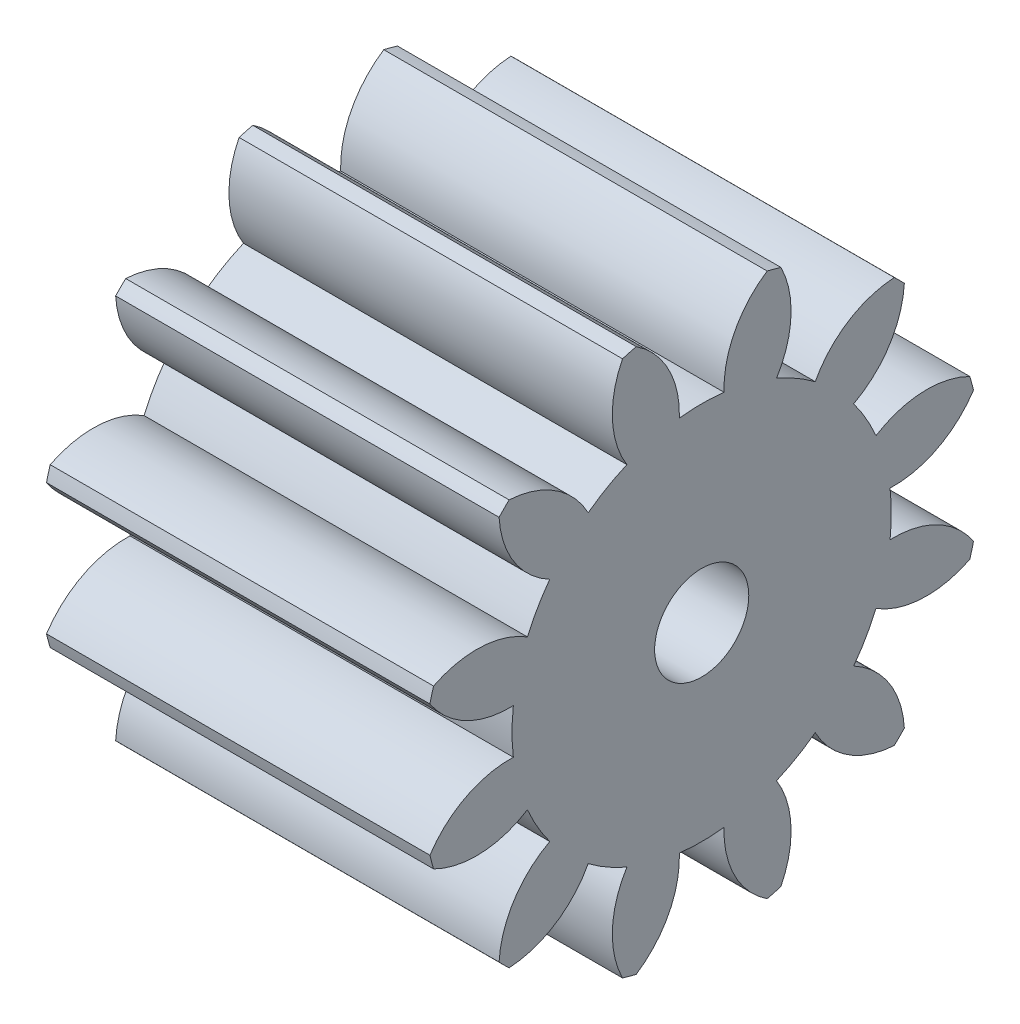
SolidWorks part; units mm, degrees
ref_plane "Plane1" through (0, 0, 0) normal (0, 0, 1) x (1, 0, 0)
ref_plane "Plane2" through (0, 0, 0) normal (0, 1, 0) x (1, 0, 0)
ref_plane "Plane3" through (0, 0, 0) normal (1, 0, 0) x (0, 0, -1)
sketch "HoldingSke" plane through (0, 0, 0) normal (0, 1, 0) x (1, 0, 0)
  line L0 (0, 0) -> (0.7825, -0.1663)
  line L1 (-15, 0) -> (100, 0) construction
  line L2 (0, 0) -> (-2.1039, 2.3779)
  line L3 (0, 0) -> (-11.863, 4.5341)
  line L4 (0, 0) -> (8.4473, 1.7955)
  line L5 (0, 0) -> (-46.8476, -17.4728)
  line L6 (0, 0) -> (-9.9476, -6.7116)
  line L7 (-2.1039, 2.3779) -> (8.6586, 51.2059)
  line L8 (-76.2, 54.61) -> (-76.1, 54.61)
  line L9 (-71.009, 38.7566) -> (-53.1078, 45.2721)
  line L10 (-76.2, 71.12) -> (104.1128, 71.12)
  line L11 (0, 0) -> (-12, 0)
  line L12 (-76.2, 101.6) -> (-76.155, 101.6)
  line L13 (24.9733, 27.94) -> (52.9518, 28.4284)
  line L14 (24.9733, 27.94) -> (24.9743, 27.94)
  line L15 (24.9733, 27.94) -> (100.4006, 29.5858)
  line L16 (-63.627, -1.25) -> (-12.827, -1.25)
  circle A0 centre (0, 0) radius 0.4
  circle A1 centre (0, 0) radius 5.9365
  circle A2 centre (0, 0) radius 37.5
  circle A3 centre (0, 0) radius 0.4
  dimension "MHD" = 11.873
  dimension "Hub_dia" = 75
  dimension "Bore" = 0.8
  dimension "MBD" = 0.8
  dimension "Num_teeth" = 12
  dimension "Pitch_radius" = 180.3128
  dimension "Pitch" = 0.8
  dimension "Width" = 12
  dimension "Overall_len" = 50
  dimension "Show_teeth" = 12
  dimension "Thickness" = 12
  dimension "OAL" = 50.0001
  dimension "T_dim" = 0.1
  dimension "Ap" = 20
  dimension "H" = 19.05
  dimension "Backlash" = 0.045
  dimension "Addendum_fac" = 1
  dimension "Dedendum_fac" = 1.25
  dimension "Clearance_fac" = 0.25
  dimension "Dedendum_add" = 0.001
  dimension "Module" = 1.25
sketch "BasProSke" plane through (0, 0, 0) normal (0, 1, 0) x (1, 0, 0)
  line L0 (-10, 0) -> (60, 0) construction
  line L1 (0, 0) -> (0, 8.75)
  line L2 (0, 0) -> (12, 0)
  line L3 (12, 0) -> (12, 8.75)
  line L4 (12, 8.75) -> (0, 8.75)
  dimension "Diameter" = 17.5
  dimension "Thickness" = 12
revolve "Base-Revolve" add sketch "BasProSke" angle 360 about L0
sketch "TooCutSke" plane through (0, 0, 0) normal (1, 0, 0) x (0, 0, -1)
  line L1 (0, 0) -> (0, 107) construction
  line L2 (0, 0) -> (-1.0576, 7.4251) construction
  line L3 (0, 0) -> (-3.8542, 14.3841) construction
  line L4 (-1.0576, 7.4251) -> (-1.9271, 7.1921) construction
  arc A0 (0.6993, 5.8952) -> (-0.6993, 5.8952) centre (0, 0) ccw
  arc A1 (2.0786, 8.5257) -> (-2.0786, 8.5257) centre (0, 0) ccw
  circle A2 centre (0, 0) radius 7.5 construction
  circle A3 centre (0, 0) radius 7.0477 construction
  arc A4 (-0.6993, 5.8952) -> (-2.0786, 8.5257) centre (-3.6975, 5.9999) ccw
  arc A5 (2.0786, 8.5257) -> (0.6993, 5.8952) centre (3.6975, 5.9999) ccw
  dimension "Root_dia" = 11.873
  dimension "Overcut_dia" = 17.5508
  dimension "Pitch_dia" = 15
  dimension "Base_dia" = 14.0954
  dimension "Flank_rad" = 3
  dimension "Half_ang" = 15
  dimension "Half_CT" = 0.9002
extrude "ToothCut" cut sketch "TooCutSke" along normal through all
fillet "Breaks" [suppressed] radius 0.025
fillet "RootFillets" [suppressed] radius 0.3135
pattern_circular "TeethCuts" count 12 every 30 about axis through (-10, 0, 0) along (1, 0, 0) of "ToothCut", "RootFillets", "Breaks"
sketch "HubNeaOneSke" plane through (0, 0, 0) normal (-1, 0, 0) x (0, 0, 1)
  circle A0 centre (0, 0) radius 5.9365
  dimension "Diameter" = 11.873
extrude "HubNearOne" [suppressed] add sketch "HubNeaOneSke" along normal blind 38.0001
sketch "HubNeaBotSke" plane through (0, 0, 0) normal (-1, 0, 0) x (0, 0, 1)
  circle A0 centre (0, 0) radius 5.9365
  dimension "Diameter" = 11.873
extrude "HubNearBoth" [suppressed] add sketch "HubNeaBotSke" along normal blind 19
ref_plane "FarPln" through (12, 0, 0) normal (1, 0, 0) x (0, 0, -1)
sketch "HubFarSke" plane through (12, 0, 0) normal (1, 0, 0) x (0, 0, -1)
  circle A0 centre (0, 0) radius 5.9365
  dimension "Diameter" = 11.873
extrude "HubFar" [suppressed] add sketch "HubFarSke" along normal blind 19
sketch "BorSke" plane through (0, 0, 0) normal (1, 0, 0) x (0, 0, -1)
  circle A0 centre (0, 0) radius 0.4
  dimension "Diameter" = 0.8
extrude "Bore" cut sketch "BorSke" along normal mid plane 100.0001
sketch "KeySke" plane through (0, 0, 0) normal (1, 0, 0) x (0, 0, -1)
  line L0 (-0.05, 0) -> (-0.05, 0.5)
  line L1 (-0.05, 0.5) -> (0.05, 0.5)
  line L2 (0.05, 0.5) -> (0.05, 0)
  line L3 (0, 0) -> (0, 34) construction
  line L4 (-0.05, 0) -> (0.05, 0)
  dimension "Offset" = 0.5
  dimension "Width" = 0.1
extrude "Keyway" [suppressed] cut sketch "KeySke" along normal mid plane 100.0001
pattern_circular "Keyway2" [suppressed] count 2 every 90 about axis through (-10, 0, 0) along (1, 0, 0)
sketch "Sketch3" plane through (12, 0, 0) normal (1, 0, 0) x (0, 0, -1)
  circle A0 centre (0, 0) radius 1.4732
  dimension "D1" = 2.9464
extrude "Cut-Extrude1" cut sketch "Sketch3" against normal through all
equation "' \"Module@HoldingSke\" = 6.35"
equation "' \"Num_teeth@HoldingSke\" = 12"
equation "' \"Ap@HoldingSke\" =  20"
equation "' \"Width@HoldingSke\" = 0.5 * 25.4"
equation "' \"Hub_dia@HoldingSke\"= 1 * 25.4"
equation "' \"Overall_len@HoldingSke\" = 1.0 * 25.4"
equation "' \"Bore@HoldingSke\" = 0.75 * 25.4"
equation "' \"T_dim@HoldingSke\" = 0.1 * 25.4"
equation "' \"Width@KeySke\" = 0.25 * 25.4"
equation "' \"Show_teeth@HoldingSke\" = 13"
equation "' \"Backlash@HoldingSke\" = 0.009 * 25.4"
equation "' \"Addendum_fac@HoldingSke\" = 1.0"
equation "' \"Dedendum_fac@HoldingSke\" = 1.25"
equation "' \"Dedendum_add@HoldingSke\" = 0.00005 * 25.4"
equation "' \"Clearance_fac@HoldingSke\" = 0.25"
equation "\"Pitch@HoldingSke\" = 1 / \"Module@HoldingSke\""
equation "\"Overcut_dia@TooCutSke\" = (\"Num_teeth@HoldingSke\" + 2 * \"Addendum_fac@HoldingSke\") / \"Pitch@HoldingSke\" + 0.002 * 25.4"
equation "\"Pitch_dia@TooCutSke\" = \"Num_teeth@HoldingSke\" / \"Pitch@HoldingSke\""
equation "\"Base_dia@TooCutSke\" = \"Num_teeth@HoldingSke\" / \"Pitch@HoldingSke\" * cos((\"Ap@HoldingSke\"  * 3.14159265 / 180))"
equation "\"Root_dia@TooCutSke\" = (\"Num_teeth@HoldingSke\" + 2) / \"Pitch@HoldingSke\" - 2 * (\"Addendum_fac@HoldingSke\" + \"Dedendum_fac@HoldingSke\") / \"Pitch@HoldingSke\" - \"Dedendum_add@HoldingSke\" * 2"
equation "\"Half_ang@TooCutSke\" = 180 / \"Num_teeth@HoldingSke\""
equation "\"Half_CT@TooCutSke\" = \"Num_teeth@HoldingSke\" / \"Pitch@HoldingSke\" * sin((3.14159265 / 2 / \"Num_teeth@HoldingSke\")) / 2 - 7 * \"Backlash@HoldingSke\" / 4"
equation "\"Flank_rad@TooCutSke\" = \"Num_teeth@HoldingSke\" / \"Pitch@HoldingSke\" / 5"
equation "\"Radius@RootFillets\" = \"Clearance_fac@HoldingSke\" / \"Pitch@HoldingSke\" + \"Dedendum_add@HoldingSke\""
equation "\"Break_rad@Breaks\" = 0.02 / \"Pitch@HoldingSke\""
equation "\"Thickness@HoldingSke\" = \"Width@HoldingSke\""
equation "\"OAL@HoldingSke\" = \"Thickness@HoldingSke\""
equation "\"MHD@HoldingSke\" = (\"Num_teeth@HoldingSke\" + 2) / \"Pitch@HoldingSke\" - 2 * (\"Addendum_fac@HoldingSke\" + \"Dedendum_fac@HoldingSke\")  / \"Pitch@HoldingSke\" - \"Dedendum_add@HoldingSke\" * 2"
equation "\"MBD@HoldingSke\" = (\"Num_teeth@HoldingSke\" + 2) / \"Pitch@HoldingSke\" - 2 * (\"Addendum_fac@HoldingSke\" + \"Dedendum_fac@HoldingSke\")  / \"Pitch@HoldingSke\" - \"Dedendum_add@HoldingSke\" * 2 - 0.002 * 25.4"
equation "\"MHD@HoldingSke\" = ((sgn( \"MHD@HoldingSke\" - \"Hub_dia@HoldingSke\" )-1)*( \"MHD@HoldingSke\" - \"Hub_dia@HoldingSke\" ))/-2+ \"Hub_dia@HoldingSke\""
equation "\"MBD@HoldingSke\" = ((sgn( \"MBD@HoldingSke\" - \"Bore@HoldingSke\" )-1)*( \"MBD@HoldingSke\" - \"Bore@HoldingSke\" ))/-2+ \"Bore@HoldingSke\""
equation "\"OAL@HoldingSke\" = ((sgn( \"OAL@HoldingSke\" - \"Overall_len@HoldingSke\" )+1)*( \"OAL@HoldingSke\" - \"Overall_len@HoldingSke\" ))/2 + \"Overall_len@HoldingSke\" + 0.000002 * 25.4"
equation "\"Num_teeth@TeethCuts\" = int( \"Show_teeth@HoldingSke\" ) + 1"
equation "\"Num_teeth@TeethCuts\" = ((sgn( \"Num_teeth@TeethCuts\" - \"Num_teeth@HoldingSke\" )-1)*( \"Num_teeth@TeethCuts\" - \"Num_teeth@HoldingSke\" ))/-2+ \"Num_teeth@HoldingSke\""
equation "\"Num_teeth@TeethCuts\" = ((sgn( \"Num_teeth@TeethCuts\" - 2.0)+1)*( \"Num_teeth@TeethCuts\" - 2.0))/2 +2.0"
equation "\"Angle@TeethCuts\" = 360.0 / \"Num_teeth@HoldingSke\""
equation "\"Diameter@BasProSke\" = (\"Num_teeth@HoldingSke\" + 2 * \"Addendum_fac@HoldingSke\") / \"Pitch@HoldingSke\""
equation "\"Thickness@BasProSke\"  = \"Thickness@HoldingSke\""
equation "' \"Fillet_rad@BasProSke\" =  \"Thickness@HoldingSke\" * 0.05"
equation "\"MHD@HoldingSke\" = ((sgn( \"MHD@HoldingSke\" - \"Root_dia@TooCutSke\" )-1)*( \"MHD@HoldingSke\" - \"Root_dia@TooCutSke\" ))/-2+ \"Root_dia@TooCutSke\""
equation "\"Diameter@HubNeaOneSke\" = \"MHD@HoldingSke\""
equation "\"Length@HubNearOne\" = \"OAL@HoldingSke\" - \"Thickness@BasProSke\""
equation "\"Diameter@HubNeaBotSke\" = \"MHD@HoldingSke\""
equation "\"Length@HubNearBoth\" = ( \"OAL@HoldingSke\" - \"Thickness@BasProSke\" ) / 2.0"
equation "\"Thickness@FarPln\" = \"Thickness@BasProSke\""
equation "\"Diameter@HubFarSke\" = \"MHD@HoldingSke\""
equation "\"Length@HubFar\" = ( \"OAL@HoldingSke\" - \"Thickness@BasProSke\" ) / 2.0"
equation "\"Diameter@BorSke\" = \"MBD@HoldingSke\""
equation "\"D1@Bore\" = \"OAL@HoldingSke\" * 2.0"
equation "\"D1@Keyway\" = \"OAL@HoldingSke\" * 2.0"
equation "\"Offset@KeySke\" = \"T_dim@HoldingSke\" + \"MBD@HoldingSke\" / 2.0"
